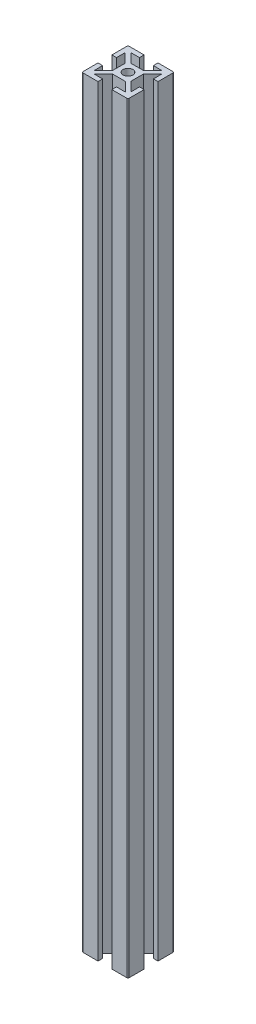
SolidWorks part; units mm, degrees
material "6061 Alloy"
ref_plane "Front Plane" through (0, 0, 0) normal (0, 0, 1) x (1, 0, 0)
ref_plane "Top Plane" through (0, 0, 0) normal (0, 1, 0) x (1, 0, 0)
ref_plane "Right Plane" through (0, 0, 0) normal (1, 0, 0) x (0, 0, -1)
ref_plane "Plane1" through (0, 420, 0) normal (0, 1, 0) x (1, 0, 0)
sketch "Sketch1" plane through (0, 420, 0) normal (0, 1, 0) x (1, 0, 0)
  line L0 (4, 2.7464) -> (8, 6.7464)
  line L1 (8, 6.7464) -> (8, 3)
  line L2 (8, 3) -> (10, 3)
  line L3 (10, 3) -> (10, 9.5)
  line L4 (9.5, 10) -> (3, 10)
  line L5 (3, 10) -> (3, 8)
  line L6 (3, 8) -> (6.8633, 8)
  line L7 (6.8633, 8) -> (2.8633, 4)
  line L8 (2.8633, 4) -> (-2.75, 4)
  line L9 (-2.75, 4) -> (-6.75, 8)
  line L10 (-6.75, 8) -> (-3, 8)
  line L11 (-3, 8) -> (-3, 10)
  line L12 (-3, 10) -> (-9.5, 10)
  line L13 (-10, 9.5) -> (-10, 3)
  line L14 (-10, 3) -> (-8, 3)
  line L15 (-8, 3) -> (-8, 6.75)
  line L16 (-8, 6.75) -> (-4, 2.75)
  line L17 (-4, 2.75) -> (-4, -2.75)
  line L18 (-4, -2.75) -> (-8, -6.75)
  line L19 (-8, -6.75) -> (-8, -3)
  line L20 (-8, -3) -> (-10, -3)
  line L21 (-10, -3) -> (-10, -9.5)
  line L22 (-9.5, -10) -> (-3, -10)
  line L23 (-3, -10) -> (-3, -8)
  line L24 (-3, -8) -> (-6.75, -8)
  line L25 (-6.75, -8) -> (-2.75, -4)
  line L26 (-2.75, -4) -> (2.8685, -4)
  line L27 (2.8685, -4) -> (6.8685, -8)
  line L28 (6.8685, -8) -> (3, -8)
  line L29 (3, -8) -> (3, -10)
  line L30 (3, -10) -> (9.5, -10)
  line L31 (10, -9.5) -> (10, -3)
  line L32 (10, -3) -> (8, -3)
  line L33 (8, -3) -> (8, -6.6652)
  line L34 (8, -6.6652) -> (4, -2.6652)
  line L35 (4, -2.6652) -> (4, 2.7464)
  arc A0 (10, 9.5) -> (9.5, 10) centre (9.5, 9.5) ccw
  arc A1 (-9.5, 10) -> (-10, 9.5) centre (-9.5, 9.5) ccw
  arc A2 (-10, -9.5) -> (-9.5, -10) centre (-9.5, -9.5) ccw
  arc A3 (9.5, -10) -> (10, -9.5) centre (9.5, -9.5) ccw
  circle A4 centre (0, 0) radius 2.1
extrude "Boss-Extrude1" add sketch "Sketch1" against normal blind 330
ref_plane "Plane2" through (0, 0, 0) normal (1, 0, 0) x (0, 0, -1)
ref_plane "Plane3" through (0, 0, 0) normal (0, 0, 1) x (1, 0, 0)
